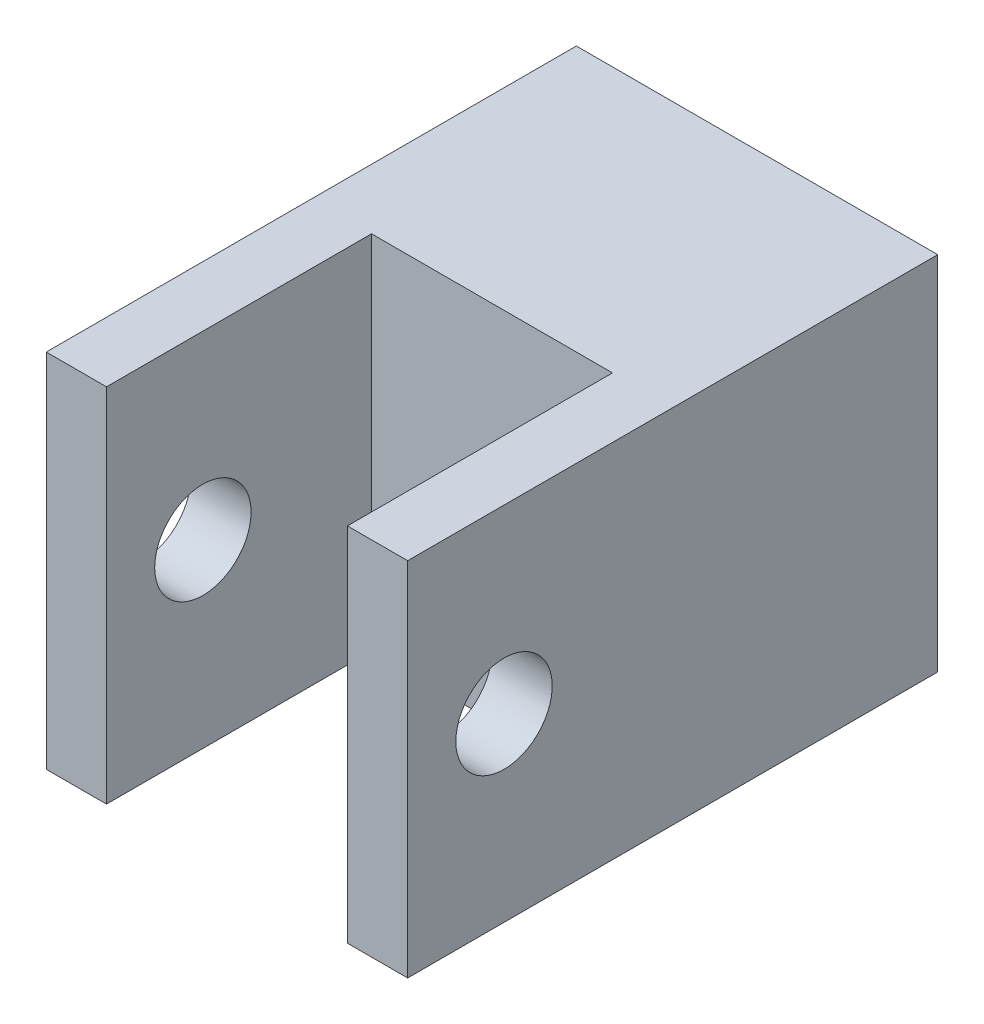
SolidWorks part; units mm, degrees
ref_plane "Front Plane" through (0, 0, 0) normal (0, 0, 1) x (1, 0, 0)
ref_plane "Top Plane" through (0, 0, 0) normal (0, 1, 0) x (1, 0, 0)
ref_plane "Right Plane" through (0, 0, 0) normal (1, 0, 0) x (0, 0, -1)
sketch "Sketch2" plane through (0, 0, 0) normal (0, 0, 1) x (1, 0, 0)
  line L1 (-7.5, -7.5) -> (7.5, -7.5)
  line L2 (-7.5, -7.5) -> (-7.5, 7.5)
  line L3 (-7.5, 7.5) -> (7.5, 7.5)
  line L4 (7.5, -7.5) -> (7.5, 7.5)
  line L5 (-7.5, -7.5) -> (7.5, 7.5) construction
  line L6 (-7.5, 7.5) -> (7.5, -7.5) construction
  point P0 (0, 0)
  dimension "D1" = 15
  dimension "D2" = 15
extrude "Boss-Extrude2" add sketch "Sketch2" along normal blind 22
sketch "Sketch4" plane through (0, 0, 22) normal (0, 0, 1) x (1, 0, 0)
  line L0 (7.5, 7.5) -> (-7.5, 7.5) construction
  line L1 (5, -7.5) -> (-5, -7.5)
  line L2 (5, -7.5) -> (5, 7.5)
  line L3 (5, 7.5) -> (-5, 7.5)
  line L4 (-5, -7.5) -> (-5, 7.5)
  line L5 (5, -7.5) -> (-5, 7.5) construction
  line L6 (5, 7.5) -> (-5, -7.5) construction
  point P0 (0, 0)
  dimension "D1" = 10
extrude "Cut-Extrude1" cut sketch "Sketch4" against normal blind 11 contours L2 L1 L4 L3
sketch "Sketch5" plane through (-7.5, 0, 0) normal (-1, 0, 0) x (0, 0, 1)
  line L0 (22, -7.5) -> (11, -7.5) construction
  line L1 (22, -7.5) -> (0, -7.5) construction
  line L4 (18, 0) -> (22, 0) construction
  line L5 (22, 7.5) -> (22, -7.5) construction
  circle A0 centre (18, 0) radius 2
  dimension "D1" = 4
  dimension "D2" = 4
extrude "Cut-Extrude2" cut sketch "Sketch5" against normal blind 25
